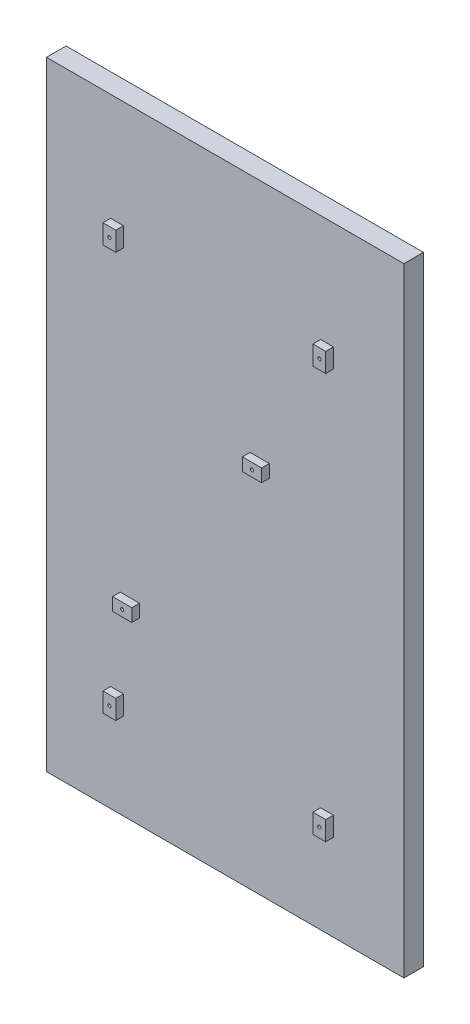
SolidWorks part; units mm, degrees
ref_plane "Front Plane" through (0, 0, 0) normal (0, 0, 1) x (1, 0, 0)
ref_plane "Top Plane" through (0, 0, 0) normal (0, 1, 0) x (1, 0, 0)
ref_plane "Right Plane" through (0, 0, 0) normal (1, 0, 0) x (0, 0, -1)
sketch "Sketch1" plane through (0, 0, 0) normal (0, 0, 1) x (1, 0, 0)
  line L0 (0, 0) -> (0, 193)
  line L1 (0, 193) -> (111.5, 193)
  line L2 (111.5, 193) -> (111.5, 0)
  line L3 (111.5, 0) -> (0, 0)
extrude "Boss-Extrude1" add sketch "Sketch1" along normal blind 6.1
sketch "Sketch2" plane through (0, 0, 6.1) normal (0, 0, 1) x (1, 0, 0)
  line L1 (20, 159.5) -> (24, 159.5)
  line L7 (87.5, 33) -> (85.5, 33)
  line L8 (85.5, 33) -> (85.5, 27)
  line L9 (85.5, 27) -> (89.5, 27)
  line L10 (89.5, 27) -> (89.5, 33)
  line L11 (89.5, 33) -> (87.5, 33)
  line L12 (20, 33) -> (24, 33)
  line L13 (20, 33) -> (20, 27)
  line L14 (20, 27) -> (24, 27)
  line L15 (24, 33) -> (24, 27)
  line L16 (20, 159.5) -> (20, 153.5)
  line L17 (20, 153.5) -> (24, 153.5)
  line L18 (24, 159.5) -> (24, 153.5)
  line L19 (85.5, 159.5) -> (89.5, 159.5)
  line L20 (85.5, 159.5) -> (85.5, 153.5)
  line L21 (85.5, 153.5) -> (89.5, 153.5)
  line L22 (89.5, 159.5) -> (89.5, 153.5)
  line L23 (23, 60) -> (29, 60)
  line L24 (23, 60) -> (23, 56)
  line L25 (23, 56) -> (29, 56)
  line L26 (29, 60) -> (29, 56)
  line L27 (63.5, 118) -> (69.5, 118)
  line L28 (63.5, 118) -> (63.5, 114)
  line L29 (63.5, 114) -> (69.5, 114)
  line L30 (69.5, 118) -> (69.5, 114)
  circle A0 centre (22, 30) radius 0.5
  circle A1 centre (26, 58) radius 0.5
  circle A2 centre (87.5, 30) radius 0.5
  circle A3 centre (66.5, 116) radius 0.5
  circle A4 centre (22, 156.5) radius 0.5
  circle A5 centre (87.5, 156.5) radius 0.5
  point P0 (22, 30)
  point P1 (87.5, 30)
  point P2 (87.5, 156.5)
  point P3 (22, 156.5)
  point P4 (24, 153.5)
  point P5 (24, 27)
  point P6 (20, 159.5)
  point P8 (20, 33)
  point P21 (85.5, 159.5)
  point P24 (89.5, 153.5)
  point P27 (29, 56)
  point P28 (66.5, 58)
  point P29 (26, 116)
  point P30 (66.5, 116)
  point P31 (23, 60)
  point P32 (66.5, 116)
  point P33 (63.5, 118)
  point P34 (26, 58)
  point P36 (69.5, 114)
extrude "Boss-Extrude2" add sketch "Sketch2" along normal blind 2.4
sketch "Sketch3" plane through (0, 0, 6.1) normal (0, 0, 1) x (1, 0, 0)
  text T0 "Ribbon Side\r\n"
  text T1 "HDMI\r\n"
